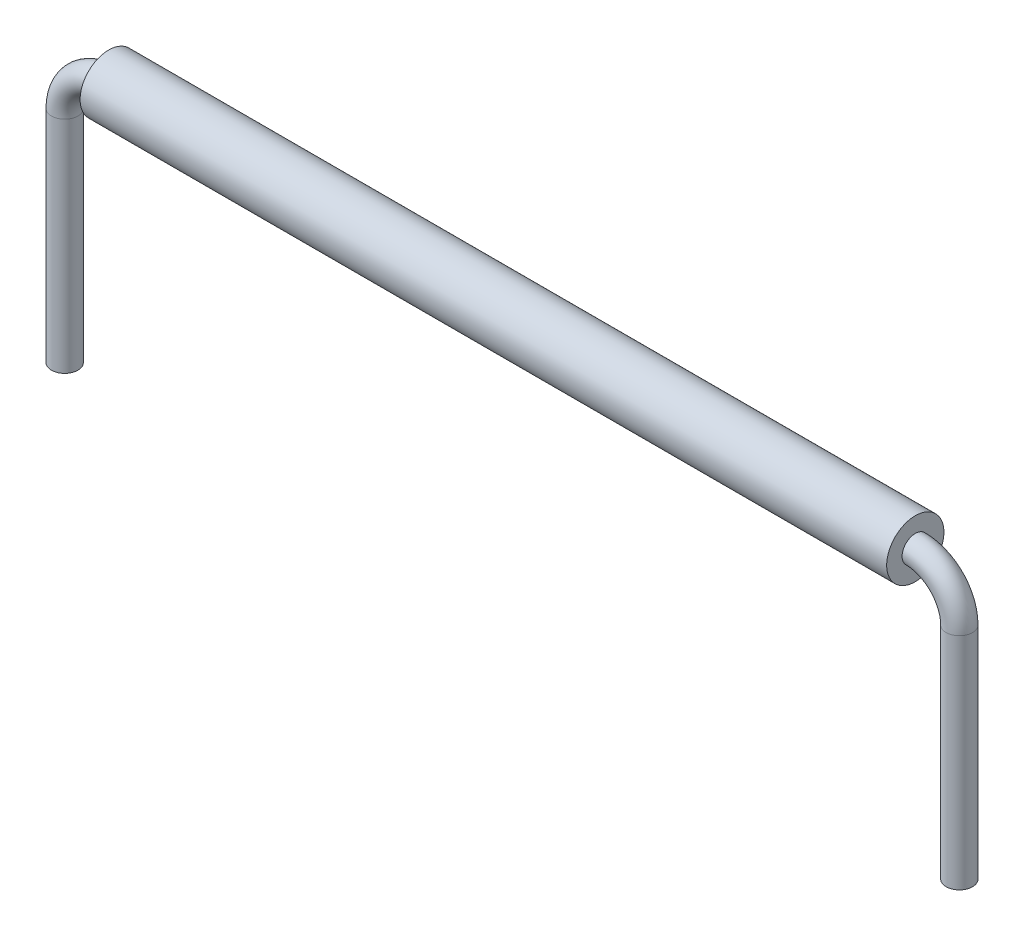
SolidWorks part; units mm, degrees
other "Wire"
other "Insulation"
ref_plane "Front Plane" through (0, 0, 0) normal (0, 0, 1) x (1, 0, 0)
ref_plane "Top Plane" through (0, 0, 0) normal (0, 1, 0) x (1, 0, 0)
ref_plane "Right Plane" through (0, 0, 0) normal (1, 0, 0) x (0, 0, -1)
sketch "Sketch1" plane through (0, 0, 0) normal (0, 0, 1) x (1, 0, 0)
  line L0 (-9.16, 0) -> (9.16, 0)
  line L1 (-10.16, -1) -> (-10.16, -6)
  line L2 (10.16, -1) -> (10.16, -6)
  line L3 (0, 0) -> (0, -6) construction
  line L4 (-10.16, -6) -> (10.16, -6) construction
  arc A0 (-9.16, 0) -> (-10.16, -1) centre (-9.16, -1) ccw
  arc A1 (9.16, 0) -> (10.16, -1) centre (9.16, -1) cw
  dimension "D1" = 1
  dimension "D2" = 20.32
  dimension "D3" = 6
sketch "Sketch2" plane through (0, 0, 0) normal (1, 0, 0) x (0, 0, -1)
  circle A0 centre (0, 0) radius 0.3
  dimension "D1" = 0.6
sweep "Sweep1" add profiles "Sketch2" path "Sketch1"
sketch "Sketch3" plane through (0, 0, 0) normal (1, 0, 0) x (0, 0, -1)
  circle A0 centre (0, 0) radius 0.65
  circle A1 centre (0, 0) radius 0.3
  dimension "D1" = 1.3
  dimension "D2" = 0.6
extrude "Boss-Extrude1" add sketch "Sketch3" along normal up to vertex (9.16 mm away) and the other way up to vertex (9.16 mm away) separate body up to point (9.16, 0, 0) other way up to point (-9.16, 0, 0)
